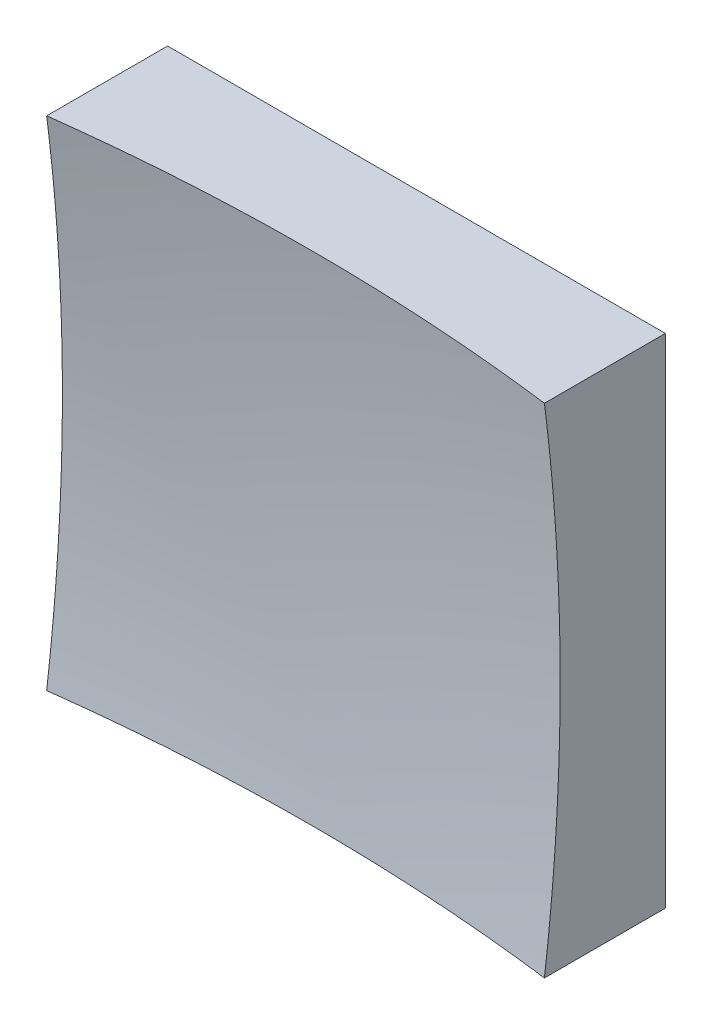
SolidWorks part; units mm, degrees
ref_plane "前视基准面" through (0, 0, 0) normal (0, 0, 1) x (1, 0, 0)
ref_plane "上视基准面" through (0, 0, 0) normal (0, 1, 0) x (1, 0, 0)
ref_plane "右视基准面" through (0, 0, 0) normal (1, 0, 0) x (0, 0, -1)
sketch "草图1" plane through (0, 0, 0) normal (0, 0, 1) x (1, 0, 0)
  line L1 (-25, 25) -> (25, 25)
  line L2 (-25, 25) -> (-25, -25)
  line L3 (-25, -25) -> (25, -25)
  line L4 (25, 25) -> (25, -25)
  line L5 (-25, 25) -> (25, -25) construction
  line L6 (-25, -25) -> (25, 25) construction
  point P0 (0, 0)
  dimension "D1" = 50
  dimension "D2" = 50
extrude "凸台-拉伸1" add sketch "草图1" along normal blind 50 contours L2 L3 L4 L1
sketch "草图2" plane through (0, 0, 0) normal (0, 1, 0) x (1, 0, 0)
  line L0 (-7.4603, -9) -> (7.3192, -9) construction
  line L1 (0, 0) -> (0, -12.1749) construction
  line L2 (194.9691, -164.4236) -> (0, -164.4236)
  line L3 (0, -164.4236) -> (0, -9)
  arc A1 (194.9691, -164.4236) -> (0, -9) centre (0, -209) ccw
  dimension "D2" = 400
  dimension "D1" = 9
revolve "切除-旋转2" cut sketch "草图2" angle 360 about L3
